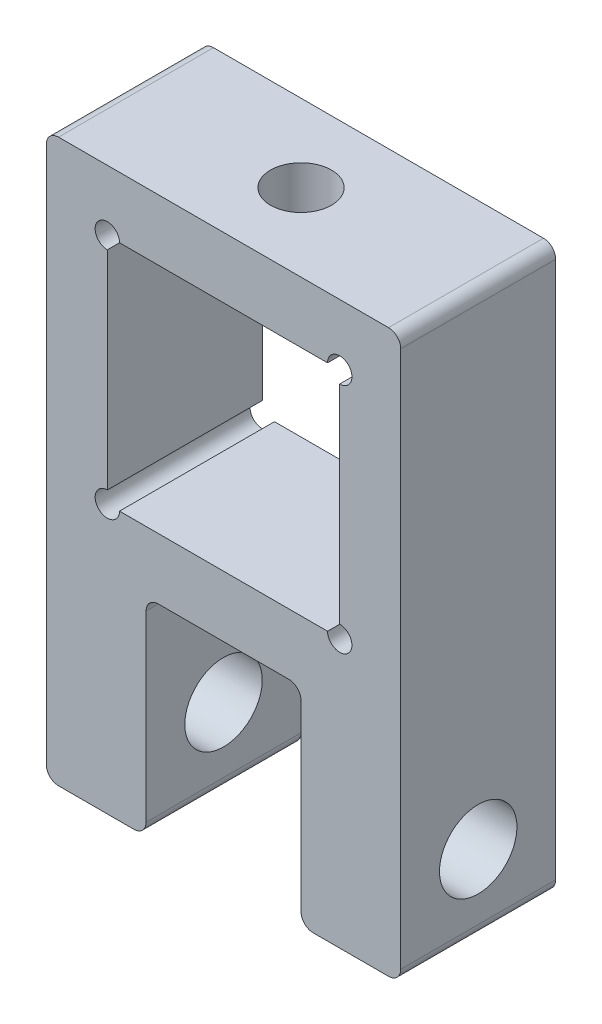
SolidWorks part; units mm, degrees
material "6061-T6 (SS)"
ref_plane "Plan de face" through (0, 0, 0) normal (0, 0, 1) x (1, 0, 0)
ref_plane "Plan de dessus" through (0, 0, 0) normal (0, 1, 0) x (1, 0, 0)
ref_plane "Plan de droite" through (0, 0, 0) normal (1, 0, 0) x (0, 0, -1)
sketch "Esquisse1" plane through (0, 0, 0) normal (0, 0, 1) x (1, 0, 0)
  line L0 (0, 0) -> (0, 79869.5619) construction
  line L1 (14.525, 46.05) -> (-14.525, 46.05)
  line L2 (-14.525, 46.05) -> (-14.525, 0)
  line L3 (-14.525, 0) -> (-6.35, 0)
  line L4 (-6.35, 0) -> (-6.35, 17)
  line L5 (-6.35, 17) -> (6.35, 17)
  line L6 (0, 17) -> (0, 22)
  line L7 (9.525, 22) -> (-9.525, 22)
  line L8 (-9.525, 22) -> (-9.525, 41.05)
  line L9 (-9.525, 41.05) -> (9.525, 41.05)
  line L10 (0, 41.05) -> (0, 46.05)
  line L11 (9.525, 22) -> (9.525, 41.05)
  line L12 (6.35, 0) -> (6.35, 17)
  line L13 (14.525, 0) -> (6.35, 0)
  line L14 (14.525, 46.05) -> (14.525, 0)
  circle A0 centre (-9.525, 41.05) radius 1
  circle A1 centre (-9.525, 22) radius 1
  circle A2 centre (9.525, 22) radius 1
  circle A3 centre (9.525, 41.05) radius 1
  dimension "D7" = 2
  dimension "D1" = 19.05
  dimension "D2" = 9.525
  dimension "D3" = 5
  dimension "D4" = 5
  dimension "D5" = 5
  dimension "D6" = 17
  dimension "D8" = 6.35
extrude "Boss.-Extru.1" add sketch "Esquisse1" along normal blind 12.7 contours A1 L8 A0 L9 L10 L1 L2 L3 L4 L5 L6 L7 | L9 A3 L11 A2 L7 L6 L5 L12 L13 L14 L1 L10
sketch "Esquisse2" plane through (-6.35, 0, 0) normal (1, 0, 0) x (0, 0, -1)
  line L0 (-6.35, 0) -> (-6.35, 50000) construction
  line L1 (-12.7, 0) -> (0, 0) construction
  circle A0 centre (-6.35, 6.35) radius 3.175
  point P4 (-6.35, 0)
  dimension "D1" = 6.35
  dimension "D2" = 6.35
extrude "Enlèv. mat.-Extru.1" cut sketch "Esquisse2" against normal through all both and the other way through all
fillet "Congé2" radius 1 8 edges at (14.525, 0, 6.35) (-14.525, 46.05, 6.35) (-14.525, 0, 6.35) (-6.35, 0, 6.35) (6.35, 0, 6.35) (6.35, 17, 6.35) (-6.35, 17, 6.35) (14.525, 46.05, 6.35)
sketch "Esquisse3" plane through (0, 46.05, 0) normal (0, 1, 0) x (1, 0, 0)
  line L0 (0, 0) -> (0, -12.7) construction
  line L1 (13.525, -12.7) -> (-13.525, -12.7) construction
  line L2 (-13.525, -6.35) -> (13.525, -6.35) construction
  line L3 (-13.525, 0) -> (-13.525, -12.7) construction
  line L4 (13.525, -12.7) -> (13.525, 0) construction
  circle A0 centre (0, -6.35) radius 2.5
  point P13 (0, -9.525)
  dimension "D1" = 5
extrude "Enlèv. mat.-Extru.2" cut sketch "Esquisse3" against normal up to next
